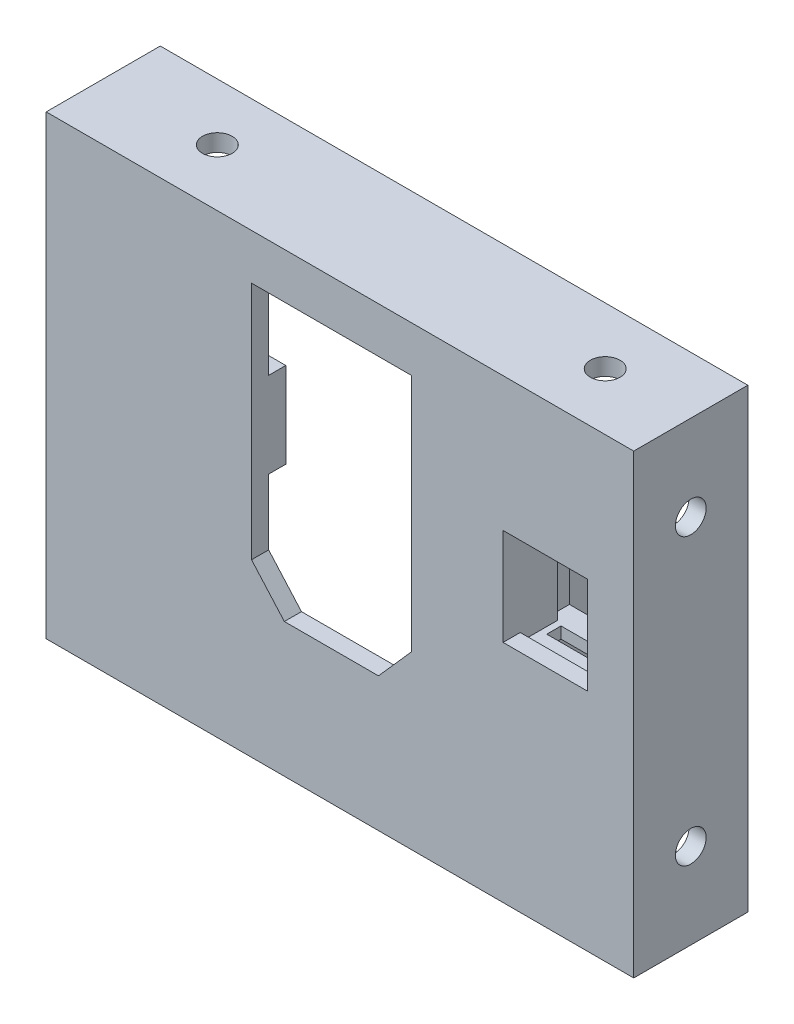
SolidWorks part; units mm, degrees
material "ABS"
ref_plane "Front Plane" through (0, 0, 0) normal (0, 0, 1) x (1, 0, 0)
ref_plane "Top Plane" through (0, 0, 0) normal (0, 1, 0) x (1, 0, 0)
ref_plane "Right Plane" through (0, 0, 0) normal (1, 0, 0) x (0, 0, -1)
sketch "Sketch1" plane through (0, 0, 0) normal (0, 0, 1) x (1, 0, 0)
  line L0 (-37.5, 0) -> (37.5, 0)
  line L1 (37.5, 0) -> (37.5, 80)
  line L2 (37.5, 80) -> (-37.5, 80)
  line L3 (-37.5, 80) -> (-37.5, 0)
  line L5 (4.25, 23.5) -> (20.75, 23.5)
  line L6 (20.75, 23.5) -> (26.5, 30)
  line L7 (26.5, 30) -> (26.5, 72)
  line L8 (26.5, 72) -> (-1.5, 72)
  line L9 (-1.5, 72) -> (-1.5, 30)
  line L10 (-1.5, 30) -> (4.25, 23.5)
  line L12 (12.5, 72) -> (12.5, 23.5) construction
  line L13 (4.25, 23.5) -> (-1.5, 23.5) construction
  line L14 (-1.5, 23.5) -> (-1.5, 30) construction
  line L15 (-1.5, 23.5) -> (26.5, 72) construction
  line L16 (37.5, 40) -> (-37.5, 40) construction
  point P2 (0, 0)
  dimension "D9" = 25
  dimension "D11" = 8
  dimension "D2" = 80
  dimension "D3" = 48.5
  dimension "D4" = 16.5
  dimension "D5" = 28
  dimension "D6" = 6.5
  dimension "D13" = 50
extrude "Boss-Extrude1" add sketch "Sketch1" along normal blind 3
sketch "Sketch2" plane through (37.5, 0, 0) normal (1, 0, 0) x (0, 0, -1)
  line L0 (-3, 80) -> (0, 80) construction
  line L1 (0, 0) -> (17, 0)
  line L3 (0, 0) -> (0, 80)
  line L4 (0, 80) -> (17, 80)
  line L5 (17, 0) -> (17, 80)
  line L6 (-3, 0) -> (-3, 80) construction
  dimension "D1" = 20
extrude "Boss-Extrude2" add sketch "Sketch2" against normal blind 3
mirror "Mirror1" about plane through (0, 0, 0) normal (1, 0, 0) of "Boss-Extrude2"
sketch "Sketch7" plane through (0, 0, 3) normal (0, 0, 1) x (1, 0, 0)
  line L0 (37.5, 80) -> (-37.5, 80) construction
  line L1 (37.5, 0) -> (62.5, 0)
  line L2 (37.5, 0) -> (37.5, 80)
  line L3 (37.5, 80) -> (62.5, 80)
  line L4 (62.5, 0) -> (62.5, 80)
  line L5 (42.6, 39.5012) -> (57.4, 39.5012)
  line L6 (42.6, 39.5012) -> (42.6, 56.5012)
  line L7 (42.6, 56.5012) -> (57.4, 56.5012)
  line L8 (57.4, 39.5012) -> (57.4, 56.5012)
  line L9 (42.6, 39.5012) -> (57.4, 56.5012) construction
  line L10 (42.6, 56.5012) -> (57.4, 39.5012) construction
  point P5 (50, 48.0012)
  dimension "D1" = 25
  dimension "D2" = 14.8
  dimension "D3" = 17
  dimension "D4" = 31.9988
  dimension "D5" = 12.5
extrude "Boss-Extrude6" add sketch "Sketch7" against normal up to surface (3 mm away) up to face at (0, 50, 0)
sketch "Sketch8" plane through (0, 0, 0) normal (0, 0, -1) x (-1, 0, 0)
  line L0 (-42.6, 56.5012) -> (-57.4, 39.5012) construction
  line L1 (-57.4, 56.5012) -> (-42.6, 39.5012) construction
  line L3 (-58.775, 38.0762) -> (-41.225, 38.0762)
  line L4 (-58.775, 38.0762) -> (-58.775, 57.9262)
  line L5 (-58.775, 57.9262) -> (-41.225, 57.9262)
  line L6 (-41.225, 38.0762) -> (-41.225, 57.9262)
  line L7 (-58.775, 38.0762) -> (-41.225, 57.9262) construction
  line L8 (-58.775, 57.9262) -> (-41.225, 38.0762) construction
  line L9 (-60.775, 36.0762) -> (-39.225, 36.0762)
  line L10 (-60.775, 36.0762) -> (-60.775, 59.9262)
  line L11 (-60.775, 59.9262) -> (-39.225, 59.9262)
  line L12 (-39.225, 36.0762) -> (-39.225, 59.9262)
  line L13 (-60.775, 36.0762) -> (-39.225, 59.9262) construction
  line L14 (-60.775, 59.9262) -> (-39.225, 36.0762) construction
  point P8 (-50, 48.0012)
  point P13 (-50, 48.0012)
  dimension "D1" = 17.55
  dimension "D2" = 19.85
  dimension "D3" = 2
  dimension "D4" = 2
extrude "Boss-Extrude7" add sketch "Sketch8" along normal blind 10
sketch "Sketch9" plane through (0, 59.9262, 0) normal (0, 1, 0) x (1, 0, 0)
  line L0 (39.225, 10) -> (60.775, 10) construction
  line L1 (43.75, 6) -> (56.25, 6)
  line L2 (43.75, 6) -> (43.75, 3.5)
  line L3 (43.75, 3.5) -> (56.25, 3.5)
  line L4 (56.25, 6) -> (56.25, 3.5)
  line L5 (43.75, 6) -> (56.25, 3.5) construction
  line L6 (43.75, 3.5) -> (56.25, 6) construction
  line L8 (62.5, -3) -> (-37.5, -3) construction
  point P0 (50, 4.75)
  point P7 (50, 10)
  dimension "D1" = 2.5
  dimension "D2" = 12.5
  dimension "D3" = 9
extrude "Cut-Extrude3" cut sketch "Sketch9" against normal up to surface (23.85 mm away) up to face at (50, 36.0762, -5)
sketch "Sketch10" plane through (0, 0, 0) normal (0, 0, -1) x (-1, 0, 0)
  line L0 (-41.225, 57.9262) -> (-58.775, 57.9262) construction
  line L1 (-41.225, 38.0762) -> (-42.6, 38.0762)
  line L2 (-41.225, 38.0762) -> (-41.225, 57.9262)
  line L3 (-41.225, 57.9262) -> (-42.6, 57.9262)
  line L4 (-42.6, 38.0762) -> (-42.6, 57.9262)
  line L5 (-42.6, 39.5012) -> (-42.6, 56.5012) construction
  line L6 (-57.4, 56.5012) -> (-57.4, 39.5012) construction
  line L7 (-58.775, 38.0762) -> (-57.4, 38.0762)
  line L8 (-58.775, 38.0762) -> (-58.775, 57.9262)
  line L9 (-58.775, 57.9262) -> (-57.4, 57.9262)
  line L10 (-57.4, 38.0762) -> (-57.4, 57.9262)
extrude "Boss-Extrude8" add sketch "Sketch10" along normal blind 6.5
sketch "Sketch11" plane through (62.5, 0, 0) normal (1, 0, 0) x (0, 0, -1)
  line L0 (7, 0) -> (7, 80) construction
  line L4 (17, 0) -> (17, 80)
  line L5 (17, 80) -> (-3, 80)
  line L6 (17, 0) -> (17, 80)
  line L8 (-3, 0) -> (17, 0)
  line L9 (-3, 80) -> (-3, 0)
  line L10 (17, 80) -> (-3, 80)
  line L13 (-3, 0) -> (17, 0)
  line L14 (-3, 80) -> (-3, 0)
  circle A0 centre (7, 15) radius 2.7
  circle A1 centre (7, 65) radius 2.7
  dimension "D3" = 15
  dimension "D4" = 15
  dimension "D5" = 5.4
  dimension "D2" = 10
  dimension "D1" = 0
extrude "Boss-Extrude9" add sketch "Sketch11" along normal blind 3
sketch "Sketch3" plane through (0, 0, 0) normal (0, 0, -1) x (-1, 0, 0)
  line L0 (-12.5, 23.5) -> (-12.5, 72) construction
  line L2 (-4.25, 23.5) -> (-20.75, 23.5) construction
  line L3 (-26.5, 72) -> (1.5, 72) construction
  line L4 (-34.5, 80) -> (-34.5, 0) construction
  line L6 (-34.5, 41.5) -> (-26.5, 41.5)
  line L7 (-34.5, 41.5) -> (-34.5, 56.5)
  line L8 (-34.5, 56.5) -> (-26.5, 56.5)
  line L9 (-26.5, 41.5) -> (-26.5, 56.5)
  line L11 (-26.5, 30) -> (-26.5, 72) construction
  line L12 (-26.5, 49) -> (-34.5, 49) construction
  line L13 (9.5, 41.5) -> (9.5, 56.5)
  line L14 (9.5, 56.5) -> (1.5, 56.5)
  line L15 (1.5, 41.5) -> (1.5, 56.5)
  line L16 (9.5, 41.5) -> (1.5, 41.5)
  dimension "D1" = 15
  dimension "D2" = 23
extrude "Boss-Extrude3" add sketch "Sketch3" along normal blind 3
sketch "Sketch5" plane through (0, 0, 0) normal (0, -1, 0) x (1, 0, 0)
  line L0 (-34.5, 0) -> (-34.5, -17)
  line L1 (-34.5, 0) -> (34.5, 0)
  line L2 (34.5, 0) -> (34.5, -17)
  line L3 (-37.5, 3) -> (-37.5, -17) construction
  line L4 (-34.5, -17) -> (34.5, -17)
  line L5 (34.5, -7) -> (-34.5, -7) construction
  line L6 (-37.5, 3) -> (65.5, 3) construction
  line L7 (34.5, -17) -> (37.5, -17) construction
  line L8 (62.5, -17) -> (37.5, -17)
  line L9 (62.5, -17) -> (62.5, 0)
  line L10 (62.5, 0) -> (37.5, 0)
  line L11 (37.5, -17) -> (37.5, 0)
  line L12 (34.5, 0) -> (34.5, -17) construction
  line L13 (62.5, 0) -> (62.5, -17) construction
  line L14 (65.5, -17) -> (62.5, -17) construction
  line L15 (65.5, 3) -> (65.5, -17) construction
  circle A0 centre (-17.5, -7) radius 2.6
  circle A1 centre (50.5, -7) radius 2.6
  dimension "D2" = 5.2
  dimension "D3" = 20
  dimension "D4" = 15
  dimension "D1" = 10
extrude "Boss-Extrude4" add sketch "Sketch5" against normal blind 3
ref_plane "Plane1" through (0, 40, 0) normal (0, -1, 0) x (-1, 0, 0)
mirror "Mirror2" about plane through (0, 40, 0) normal (0, -1, 0) of "Boss-Extrude4"
sketch "Sketch21" plane through (-34.5, 0, 0) normal (1, 0, 0) x (0, 0, -1)
  circle A0 centre (7, 15) radius 2.7 construction
  circle A1 centre (7, 65) radius 2.7 construction
  circle A2 centre (7, 15) radius 2.7
  circle A3 centre (7, 65) radius 2.7
extrude "Cut-Extrude5" cut sketch "Sketch21" against normal up to surface (3 mm away) up to face at (-37.5, 40, -7)
